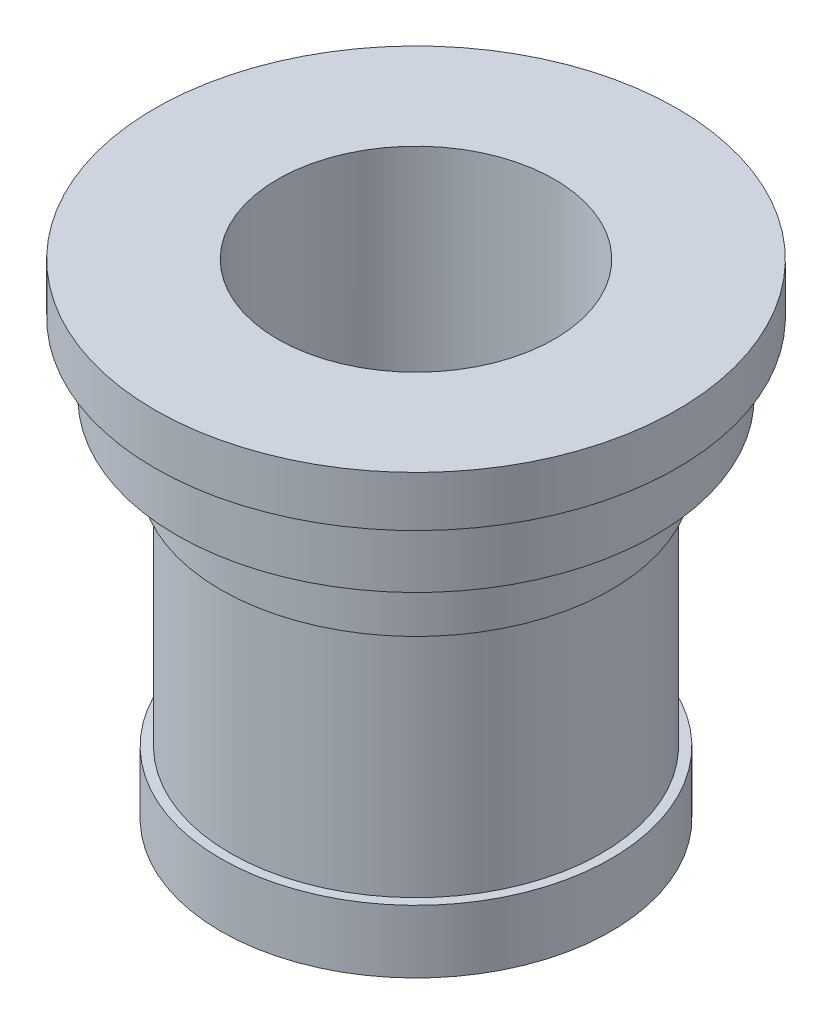
SolidWorks part; units mm, degrees
ref_plane "Front Plane" through (0, 0, 0) normal (0, 0, 1) x (1, 0, 0)
ref_plane "Top Plane" through (0, 0, 0) normal (0, 1, 0) x (1, 0, 0)
ref_plane "Right Plane" through (0, 0, 0) normal (1, 0, 0) x (0, 0, -1)
sketch "Sketch2" plane through (0, 0, 0) normal (0, 0, 1) x (1, 0, 0)
  line L0 (-31, 0) -> (-22, 0) construction
  line L1 (-22, 0) -> (-31, 0)
  line L2 (-31, 0) -> (-31, 10)
  line L3 (-31, 10) -> (-29.5, 10)
  line L4 (-29.5, 10) -> (-29.5, 47)
  line L5 (-29.5, 47) -> (-31, 47)
  line L6 (-31, 47) -> (-31, 58)
  line L7 (-31, 58) -> (-38, 58)
  line L8 (-38, 58) -> (-38, 69)
  line L9 (-38, 69) -> (-41.5, 69)
  line L10 (-41.5, 69) -> (-41.5, 77)
  line L11 (-41.5, 77) -> (-22, 77)
  line L12 (0, 108.3425) -> (0, -35.7123) construction
  line L13 (-22, 77) -> (-22, 0)
  dimension "D1" = 77
  dimension "D2" = 10
  dimension "D3" = 37
  dimension "D4" = 11
  dimension "D5" = 11
  dimension "D6" = 31
  dimension "D7" = 29.5
  dimension "D8" = 31
  dimension "D9" = 38
  dimension "D10" = 41.5
  dimension "D11" = 22
revolve "Revolve1" add sketch "Sketch2" angle 360 about L12
sketch "Sketch3" plane through (0, 0, 0) normal (0, -1, 0) x (1, 0, 0)
  circle A0 centre (-22, 0) radius 1.5
  circle A1 centre (0, 0) radius 22 construction
  dimension "D1" = 3
extrude "Cut-Extrude1" cut sketch "Sketch3" against normal blind 5
